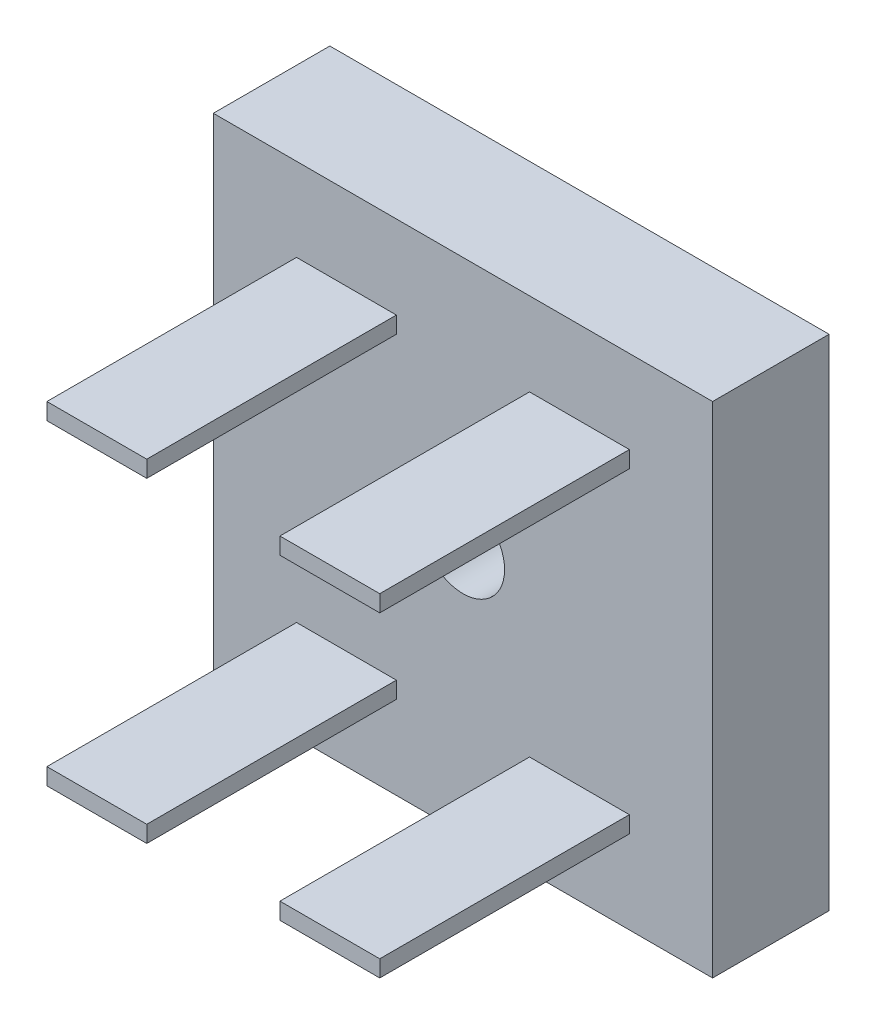
SolidWorks part; units mm, degrees
ref_plane "Plan de face" through (0, 0, 0) normal (0, 0, 1) x (1, 0, 0)
ref_plane "Plan de dessus" through (0, 0, 0) normal (0, 1, 0) x (1, 0, 0)
ref_plane "Plan de droite" through (0, 0, 0) normal (1, 0, 0) x (0, 0, -1)
sketch "Esquisse1" plane through (0, 0, 0) normal (0, 0, 1) x (1, 0, 0)
  line L1 (-3.22, 2.7172) -> (26.78, 2.7172)
  line L2 (-3.22, 2.7172) -> (-3.22, -27.2828)
  line L3 (-3.22, -27.2828) -> (26.78, -27.2828)
  line L4 (26.78, 2.7172) -> (26.78, -27.2828)
  circle A0 centre (11.78, -12.2828) radius 2.5
  point P6 (0, 0)
  point P7 (11.78, 2.7172)
  point P8 (0, 0)
  point P9 (-3.22, -12.2828)
  dimension "D2" = 5
  dimension "D1" = 30
extrude "Boss.-Extru.1" add sketch "Esquisse1" along normal blind 7
sketch "Esquisse2" plane through (0, 0, 7) normal (0, 0, 1) x (1, 0, 0)
  line L0 (7.78, -3.2828) -> (15.78, -21.2828) construction
  line L1 (1.78, -2.2828) -> (7.78, -2.2828)
  line L2 (1.78, -2.2828) -> (1.78, -3.2828)
  line L3 (1.78, -3.2828) -> (7.78, -3.2828)
  line L4 (7.78, -2.2828) -> (7.78, -3.2828)
  line L5 (15.78, -2.2828) -> (21.78, -2.2828)
  line L6 (15.78, -2.2828) -> (15.78, -3.2828)
  line L7 (15.78, -3.2828) -> (21.78, -3.2828)
  line L8 (21.78, -2.2828) -> (21.78, -3.2828)
  line L9 (1.78, -21.2828) -> (7.78, -21.2828)
  line L10 (1.78, -21.2828) -> (1.78, -22.2828)
  line L11 (1.78, -22.2828) -> (7.78, -22.2828)
  line L12 (7.78, -21.2828) -> (7.78, -22.2828)
  line L13 (15.78, -21.2828) -> (21.78, -21.2828)
  line L14 (15.78, -21.2828) -> (15.78, -22.2828)
  line L15 (15.78, -22.2828) -> (21.78, -22.2828)
  line L16 (21.78, -21.2828) -> (21.78, -22.2828)
  circle A0 centre (11.78, -12.2828) radius 2.5 construction
  point P18 (11.78, -12.2828)
  dimension "D1" = 6
  dimension "D2" = 1
  dimension "D3" = 20
  dimension "D4" = 20
extrude "Boss.-Extru.2" add sketch "Esquisse2" along normal blind 15
